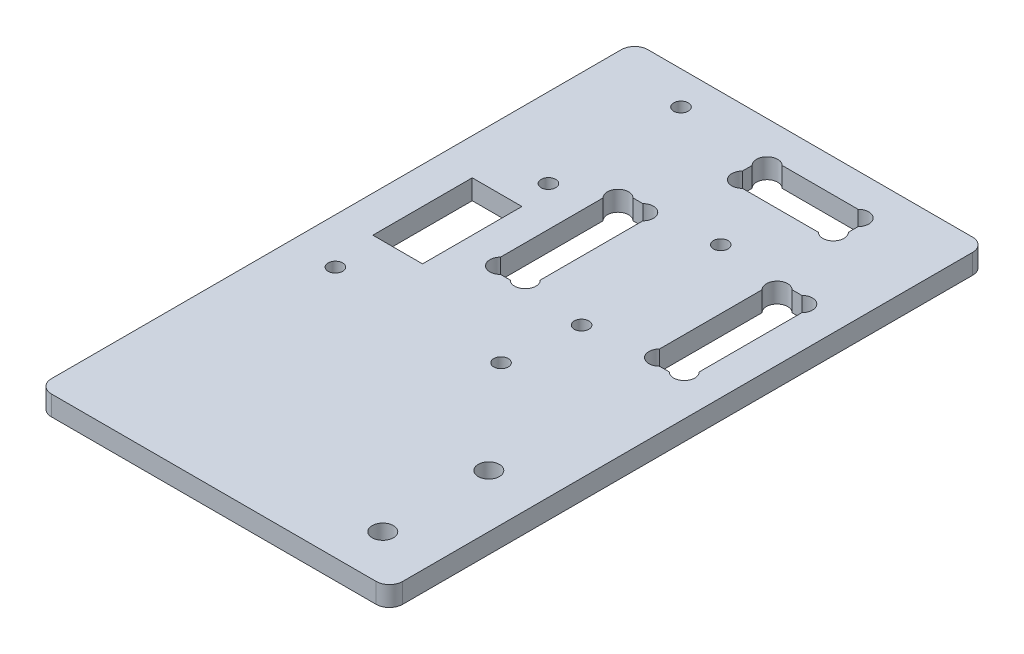
SolidWorks part; units mm, degrees
ref_plane "Plan de face" through (0, 0, 0) normal (0, 0, 1) x (1, 0, 0)
ref_plane "Plan de dessus" through (0, 0, 0) normal (0, 1, 0) x (1, 0, 0)
ref_plane "Plan de droite" through (0, 0, 0) normal (1, 0, 0) x (0, 0, -1)
sketch "Esquisse1" plane through (0, 0, 0) normal (0, 1, 0) x (1, 0, 0)
  line L6 (0, 88) -> (0, 2)
  line L7 (2, 0) -> (51, 0)
  line L8 (53, 88) -> (53, 2)
  line L11 (2, 90) -> (51, 90)
  arc A0 (51, 90) -> (53, 88) centre (51, 88) cw
  arc A1 (2, 90) -> (0, 88) centre (2, 88) ccw
  arc A2 (51, 0) -> (53, 2) centre (51, 2) ccw
  arc A3 (0, 2) -> (2, 0) centre (2, 2) ccw
  point P3 (26.5, 0)
  dimension "D3" = 2
  dimension "D5" = 2
  dimension "D4" = 2
  dimension "D1" = 53
  dimension "D2" = 90
extrude "Extrusion1" add sketch "Esquisse1" along normal blind 3
sketch "Esquisse2" plane through (0, 0, 0) normal (0, -1, 0) x (1, 0, 0)
  line L0 (53, -2) -> (53, -88) construction
  line L1 (51, -90) -> (2, -90) construction
  line L2 (2, 0) -> (51, 0) construction
  line L4 (53, -2) -> (53, -88) construction
  line L16 (41, -82.7373) -> (41, -81.2627)
  line L18 (45.7373, -49.5) -> (44.2627, -49.5)
  line L19 (45.7373, -69.5) -> (44.2627, -69.5)
  line L20 (25, -82.7373) -> (25, -81.2627)
  line L21 (38.7373, -85) -> (27.2627, -85)
  line L22 (38.7373, -79) -> (27.2627, -79)
  line L23 (48, -67.2373) -> (48, -51.7627)
  line L24 (42, -67.2373) -> (42, -51.7627)
  line L25 (24, -67.2373) -> (24, -51.7627)
  line L26 (18, -67.2373) -> (18, -51.7627)
  line L27 (20.2627, -69.5) -> (21.7373, -69.5)
  line L28 (20.2627, -49.5) -> (21.7373, -49.5)
  arc A0 (44.2627, -49.5) -> (42, -51.7627) centre (43.1314, -50.6314) ccw
  arc A1 (38.7373, -85) -> (41, -82.7373) centre (39.8686, -83.8686) ccw
  arc A2 (38.7373, -79) -> (41, -81.2627) centre (39.8686, -80.1314) cw
  arc A3 (27.2627, -85) -> (25, -82.7373) centre (26.1314, -83.8686) cw
  arc A4 (27.2627, -79) -> (25, -81.2627) centre (26.1314, -80.1314) ccw
  arc A5 (45.7373, -49.5) -> (48, -51.7627) centre (46.8686, -50.6314) cw
  arc A6 (44.2627, -69.5) -> (42, -67.2373) centre (43.1314, -68.3686) cw
  arc A7 (45.7373, -69.5) -> (48, -67.2373) centre (46.8686, -68.3686) ccw
  arc A8 (20.2627, -69.5) -> (18, -67.2373) centre (19.1314, -68.3686) cw
  arc A9 (21.7373, -69.5) -> (24, -67.2373) centre (22.8686, -68.3686) ccw
  arc A10 (20.2627, -49.5) -> (18, -51.7627) centre (19.1314, -50.6314) ccw
  arc A11 (21.7373, -49.5) -> (24, -51.7627) centre (22.8686, -50.6314) cw
  circle A12 centre (45, -23) radius 1.6
  circle A13 centre (45, -7) radius 1.6
  dimension "D15" = 2.2627
  dimension "D17" = 1.1314
  dimension "D11" = 1.6
  dimension "D32" = 3.2
  dimension "D33" = 3.2
  dimension "D1" = 6
  dimension "D2" = 6
  dimension "D3" = 6
  dimension "D4" = 18
  dimension "D5" = 20
  dimension "D6" = 16
  dimension "D7" = 5
  dimension "D8" = 1
  dimension "D9" = 9.5
  dimension "D10" = 5
  dimension "D12" = 1.1314
  dimension "D13" = 1.1314
  dimension "D14" = 2.2627
  dimension "D16" = 1.1314
  dimension "D18" = 1.1314
  dimension "D19" = 1.1314
  dimension "D20" = 2.2627
  dimension "D21" = 2.2627
  dimension "D22" = 1.1314
  dimension "D23" = 1.1314
  dimension "D24" = 1.1314
  dimension "D25" = 1.1314
  dimension "D26" = 1.1314
  dimension "D27" = 1.1314
  dimension "D28" = 2.2627
  dimension "D29" = 2.2627
  dimension "D30" = 2.2627
  dimension "D31" = 2.2627
  dimension "D34" = 16
  dimension "D35" = 7
  dimension "D36" = 8
extrude "Enlèv. mat.-Extru.1" cut sketch "Esquisse2" against normal through all
sketch "Esquisse4" plane through (0, 3, 0) normal (0, 1, 0) x (1, 0, 0)
  line L0 (51, 90) -> (2, 90) construction
  line L1 (0, 88) -> (0, 2) construction
  line L2 (53, 2) -> (53, 88) construction
  line L3 (5.5, 60) -> (13, 60)
  line L4 (5.5, 60) -> (5.5, 45)
  line L5 (5.5, 45) -> (13, 45)
  line L6 (13, 60) -> (13, 45)
  circle A0 centre (12, 85) radius 1.1
  circle A1 centre (12, 65) radius 1.1
  circle A2 centre (33, 70) radius 1.1
  circle A3 centre (33, 49) radius 1.1
  dimension "D1" = 2.2
  dimension "D2" = 5
  dimension "D4" = 12
  dimension "D14" = 2.2
  dimension "D3" = 20
  dimension "D5" = 15
  dimension "D6" = 7.5
  dimension "D7" = 5
  dimension "D8" = 1
  dimension "D10" = 20
  dimension "D12" = 20
  dimension "D13" = 21
extrude "Enlèv. mat.-Extru.2" cut sketch "Esquisse4" against normal through all
sketch "Esquisse5" plane through (0, 3, 0) normal (0, 1, 0) x (1, 0, 0)
  line L0 (0, 88) -> (0, 2) construction
  line L2 (5.5, 45) -> (13, 45) construction
  circle A0 centre (6.8474, 38) radius 1.1
  circle A1 centre (31.8474, 38) radius 1.1
  dimension "D4" = 2.2
  dimension "D1" = 6.8474
  dimension "D2" = 25
  dimension "D3" = 7
extrude "Enlèv. mat.-Extru.3" cut sketch "Esquisse5" against normal through all
